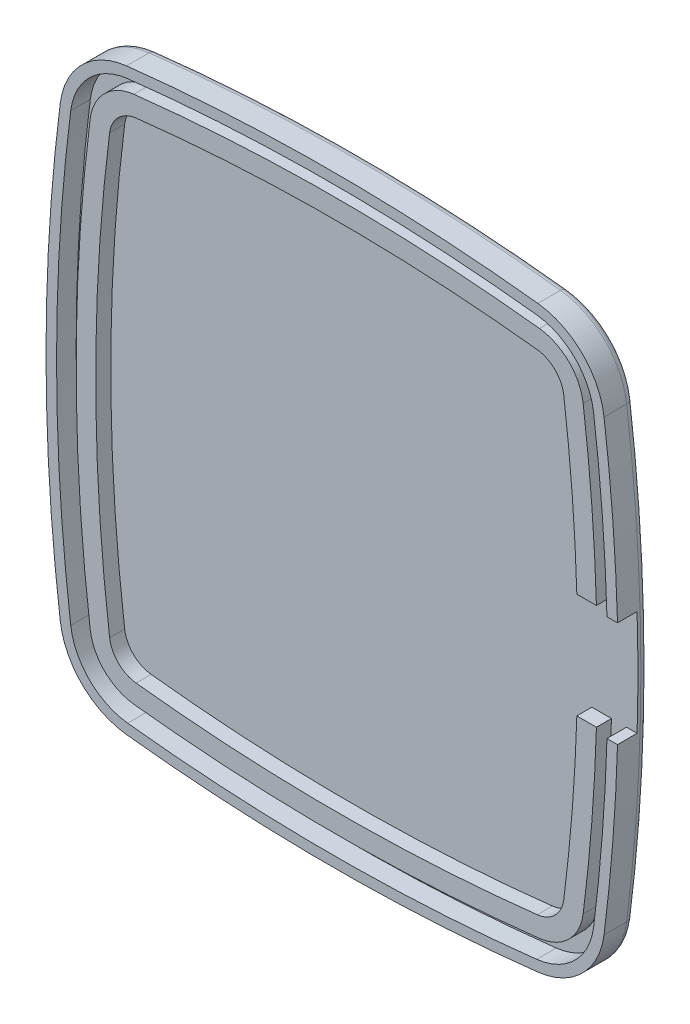
SolidWorks part; units mm, degrees
ref_plane "Ön Düzlem" through (0, 0, 0) normal (0, 0, 1) x (1, 0, 0)
ref_plane "Üst Düzlem" through (0, 0, 0) normal (0, 1, 0) x (1, 0, 0)
ref_plane "Sağ Düzlem" through (0, 0, 0) normal (1, 0, 0) x (0, 0, -1)
sketch "Çizim1" plane through (0, 0, 0) normal (0, 0, 1) x (1, 0, 0)
  line L1 (-19, -20) -> (19, -20)
  line L2 (-19, -20) -> (-19, 20)
  line L3 (-19, 20) -> (19, 20)
  line L4 (19, -20) -> (19, 20)
  line L5 (-19, -20) -> (19, 20) construction
  line L6 (-19, 20) -> (19, -20) construction
  point P0 (0, 0)
  dimension "D1" = 38
  dimension "D2" = 40
extrude "Yükseklik-Ekstrüzyon1" add sketch "Çizim1" along normal mid plane 2 contours L3 L4 L1 L2
sketch "Çizim2" plane through (0, 0, 1) normal (0, 0, 1) x (1, 0, 0)
  line L0 (-19, 18.5) -> (19, 18.5) construction
  line L1 (-19, -20) -> (-19, 20) construction
  line L2 (19, -20) -> (19, 20) construction
  line L3 (-19, 20) -> (19, 20) construction
  line L4 (0, 0) -> (12.6557, 0) construction
  line L5 (-19, 20) -> (19, 20)
  line L6 (19, 20) -> (19, 18.5)
  line L7 (-19, 20) -> (-19, 18.5)
  line L8 (-19, -18.5) -> (19, -18.5) construction
  line L9 (-19, -20) -> (-19, -18.5)
  line L10 (19, -20) -> (19, -18.5)
  line L11 (-19, -20) -> (19, -20)
  arc A0 (-19, 18.5) -> (19, 18.5) centre (0, -101.0833) cw
  arc A1 (-19, -18.5) -> (19, -18.5) centre (0, 101.0833) ccw
  line M4 (-19, 20) -> (-19, -20)
  line M5 (-19, -20) -> (19, -20)
  line M6 (19, -20) -> (19, 20)
  line M7 (19, 20) -> (-19, 20)
  dimension "D1" = 1.5
extrude "Kes-Ekstrüzyon1" cut sketch "Çizim2" against normal through all contours A0 M7 M6 | A0 L5 M4 | A1 M4 M5 | A1 L11 M6
sketch "Çizim3" plane through (0, 0, 1) normal (0, 0, 1) x (1, 0, 0)
  line L0 (17.5, 18.7287) -> (17.5, -18.7287) construction
  line L1 (19, -18.5) -> (19, 18.5) construction
  line L2 (19, 18.5) -> (19, -18.5)
  line L3 (0, 0) -> (0, -12.7146) construction
  line L4 (-17.5, 18.7287) -> (-17.5, -18.7287) construction
  line L5 (-19, 18.5) -> (-19, -18.5)
  arc A0 (19, 18.5) -> (-19, 18.5) centre (0, -101.0833) ccw construction
  arc A1 (-19, -18.5) -> (19, -18.5) centre (0, 101.0833) ccw construction
  arc A2 (17.5, 18.7287) -> (17.5, -18.7287) centre (-98.6714, 0) cw
  arc A3 (17.5, -18.7287) -> (19, -18.5) centre (0, 101.0833) ccw
  arc A4 (19, 18.5) -> (17.5, 18.7287) centre (0, -101.0833) ccw
  arc A5 (-19, 18.5) -> (-17.5, 18.7287) centre (0, -101.0833) cw
  arc A6 (-17.5, -18.7287) -> (-19, -18.5) centre (0, 101.0833) cw
  arc A7 (-17.5, 18.7287) -> (-17.5, -18.7287) centre (98.6714, 0) ccw
  arc M3 (-19, -18.5) -> (19, -18.5) centre (0, 101.0833) ccw
  line M4 (19, -18.5) -> (19, 18.5)
  arc M5 (19, 18.5) -> (-19, 18.5) centre (0, -101.0833) ccw
  line M6 (-19, 18.5) -> (-19, -18.5)
  dimension "D1" = 1.5
extrude "Kes-Ekstrüzyon2" cut sketch "Çizim3" against normal through all contours A2 L2 M5 | A2 M4 M3 | A7 L5 M3 | A7 M5 M6
fillet "Radyus1" radius 5 4 edges at (-17.5, -18.7287, 0) (17.5, -18.7287, 0) (-17.5, 18.7287, 0) (17.5, 18.7287, 0)
fillet "Radyus2" radius 0.5 8 edges at (16.605, 17.8191, -1) (0, 20, -1) (-16.605, 17.8191, -1) (-19, 0, -1) (-16.605, -17.8191, -1) (0, -20, -1) (16.605, -17.8191, -1) (19, 0, -1)
shell "İç Boşaltma1" thickness 0.7
sketch "Çizim10" plane through (0, 0, -0.3) normal (0, 0, 1) x (1, 0, 0)
  arc A0 (13.3197, 16.2464) -> (-13.3197, 16.2464) centre (0, -101.0833) ccw
  arc A1 (-13.3197, 16.2464) -> (-15.078, 14.5122) centre (-13.0941, 14.2591) ccw
  arc A2 (-15.078, 14.5122) -> (-15.078, -14.5122) centre (98.6714, 0) ccw
  arc A3 (-15.078, -14.5122) -> (-13.3197, -16.2464) centre (-13.0941, -14.2591) ccw
  arc A4 (-13.3197, -16.2464) -> (13.3197, -16.2464) centre (0, 101.0833) ccw
  arc A5 (13.3197, -16.2464) -> (15.078, -14.5122) centre (13.0941, -14.2591) ccw
  arc A6 (15.078, -14.5122) -> (15.078, 14.5122) centre (-98.6714, 0) ccw
  arc A7 (15.078, 14.5122) -> (13.3197, 16.2464) centre (13.0941, 14.2591) ccw
  arc A16 (13.4663, 17.5381) -> (-13.4663, 17.5381) centre (0, -101.0833) ccw
  arc A17 (13.4663, 17.5381) -> (-13.4663, 17.5381) centre (0, -101.0833) ccw
  arc A18 (-13.4663, 17.5381) -> (-16.3675, 14.6768) centre (-13.0941, 14.2591) ccw
  arc A19 (-13.4663, 17.5381) -> (-16.3675, 14.6768) centre (-13.0941, 14.2591) ccw
  arc A20 (-16.3675, 14.6768) -> (-16.3675, -14.6768) centre (98.6714, 0) ccw
  arc A21 (-16.3675, 14.6768) -> (-16.3675, -14.6768) centre (98.6714, 0) ccw
  arc A22 (-16.3675, -14.6768) -> (-13.4663, -17.5381) centre (-13.0941, -14.2591) ccw
  arc A23 (-16.3675, -14.6768) -> (-13.4663, -17.5381) centre (-13.0941, -14.2591) ccw
  arc A24 (-13.4663, -17.5381) -> (13.4663, -17.5381) centre (0, 101.0833) ccw
  arc A25 (-13.4663, -17.5381) -> (13.4663, -17.5381) centre (0, 101.0833) ccw
  arc A26 (13.4663, -17.5381) -> (16.3675, -14.6768) centre (13.0941, -14.2591) ccw
  arc A27 (13.4663, -17.5381) -> (16.3675, -14.6768) centre (13.0941, -14.2591) ccw
  arc A28 (16.3675, -14.6768) -> (16.3675, 14.6768) centre (-98.6714, 0) ccw
  arc A29 (16.3675, -14.6768) -> (16.3675, 14.6768) centre (-98.6714, 0) ccw
  arc A30 (16.3675, 14.6768) -> (13.4663, 17.5381) centre (13.0941, 14.2591) ccw
  arc A31 (16.3675, 14.6768) -> (13.4663, 17.5381) centre (13.0941, 14.2591) ccw
  arc A32 (13.4325, 17.24) -> (-13.4325, 17.24) centre (0, -101.0833) ccw construction
  arc A33 (-13.4325, 17.24) -> (-16.07, 14.6388) centre (-13.0941, 14.2591) ccw construction
  arc A34 (-16.07, 14.6388) -> (-16.07, -14.6388) centre (98.6714, 0) ccw construction
  arc A35 (-16.07, -14.6388) -> (-13.4325, -17.24) centre (-13.0941, -14.2591) ccw construction
  arc A36 (-13.4325, -17.24) -> (13.4325, -17.24) centre (0, 101.0833) ccw construction
  arc A37 (13.4325, -17.24) -> (16.07, -14.6388) centre (13.0941, -14.2591) ccw construction
  arc A38 (16.07, -14.6388) -> (16.07, 14.6388) centre (-98.6714, 0) ccw construction
  arc A39 (16.07, 14.6388) -> (13.4325, 17.24) centre (13.0941, 14.2591) ccw construction
  dimension "D2" = 1
  dimension "D1" = 1
extrude "Yükseklik-Ekstrüzyon10" add sketch "Çizim10" along normal blind 1 separate body
sketch "Çizim11" plane through (0, 0, -0.3) normal (0, 0, 1) x (1, 0, 0)
  line L1 (21.3654, 3.5) -> (12.6222, 3.5)
  line L2 (21.3654, 3.5) -> (21.3654, -3.5)
  line L3 (21.3654, -3.5) -> (12.6222, -3.5)
  line L4 (12.6222, 3.5) -> (12.6222, -3.5)
  arc A1 (15.078, -14.5122) -> (15.078, 14.5122) centre (-98.6714, 0) ccw construction
  point P7 (16, 0)
  dimension "D1" = 7
  dimension "D2" = 3.5
extrude "Kes-Ekstrüzyon3" cut sketch "Çizim11" along normal blind 10
sketch "Çizim12" plane through (0, 0, -0.3) normal (0, 0, 1) x (1, 0, 0)
  arc A16 (19.092, 15.3208) -> (-10.0643, 15.3208) centre (4.5138, -117.1029) ccw
  arc A17 (-10.0643, 15.3208) -> (-13.7156, 11.7508) centre (-9.6113, 11.2053) ccw
  arc A18 (-13.7156, 11.7508) -> (-13.7156, -15.7898) centre (89.9017, -2.0195) ccw
  arc A19 (-13.7156, -15.7898) -> (-10.0643, -19.3599) centre (-9.6113, -15.2444) ccw
  arc A20 (-10.0643, -19.3599) -> (19.092, -19.3599) centre (4.5138, 113.0638) ccw
  arc A21 (19.092, -19.3599) -> (22.7432, -15.7898) centre (18.6389, -15.2444) ccw
  arc A22 (22.7432, -15.7898) -> (22.7432, 11.7508) centre (-80.8741, -2.0195) ccw
  arc A23 (22.7432, 11.7508) -> (19.092, 15.3208) centre (18.6389, 11.2053) ccw
